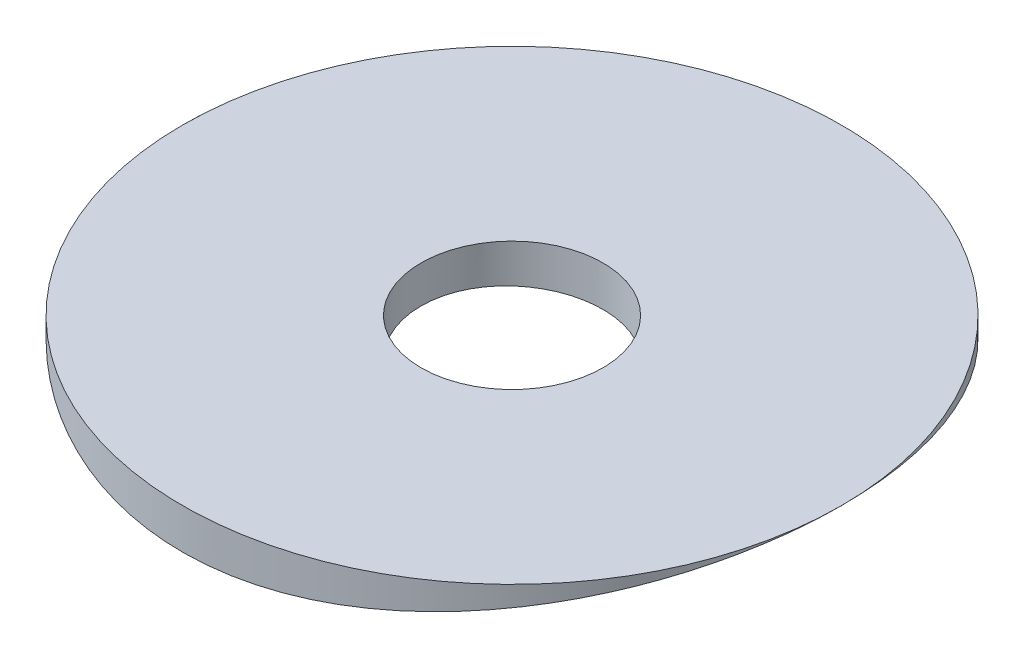
SolidWorks part; units mm, degrees
ref_plane "Front Plane" through (0, 0, 0) normal (0, 0, 1) x (1, 0, 0)
ref_plane "Top Plane" through (0, 0, 0) normal (0, 1, 0) x (1, 0, 0)
ref_plane "Right Plane" through (0, 0, 0) normal (1, 0, 0) x (0, 0, -1)
sketch "Sketch1" plane through (0, 0, 0) normal (0, 0, 1) x (1, 0, 0)
  line L0 (-11.5062, -46.2796) -> (11.5062, -46.2796)
  arc A0 (-11.5062, -46.2796) -> (11.5062, -46.2796) centre (0, 0) ccw
  dimension "D1" = 95.377
  dimension "D2" = 23.0124
extrude "Boss-Extrude1" add sketch "Sketch1" along normal blind 23.0124
sketch "Sketch2" plane through (0, -46.2796, 0) normal (0, 1, 0) x (1, 0, 0)
  line L0 (-11.5062, -23.0124) -> (11.5062, 0) construction
  line L2 (-20.1942, -31.5994) -> (24.4178, -31.5994)
  line L3 (-20.1942, -31.5994) -> (-20.1942, 9.511)
  line L4 (-20.1942, 9.511) -> (24.4178, 9.511)
  line L5 (24.4178, -31.5994) -> (24.4178, 9.511)
  circle A0 centre (0, -11.5062) radius 11.5062
extrude "Cut-Extrude3" cut sketch "Sketch2" against normal blind 2.54
sketch "Sketch3" plane through (0, -46.2796, 0) normal (0, 1, 0) x (1, 0, 0)
  circle A0 centre (0, -11.5062) radius 3.175
  arc A1 (-11.5062, -11.5062) -> (11.5062, -11.5062) centre (0, -11.5062) ccw construction
  dimension "D1" = 6.35
extrude "Cut-Extrude4" cut sketch "Sketch3" against normal through all
